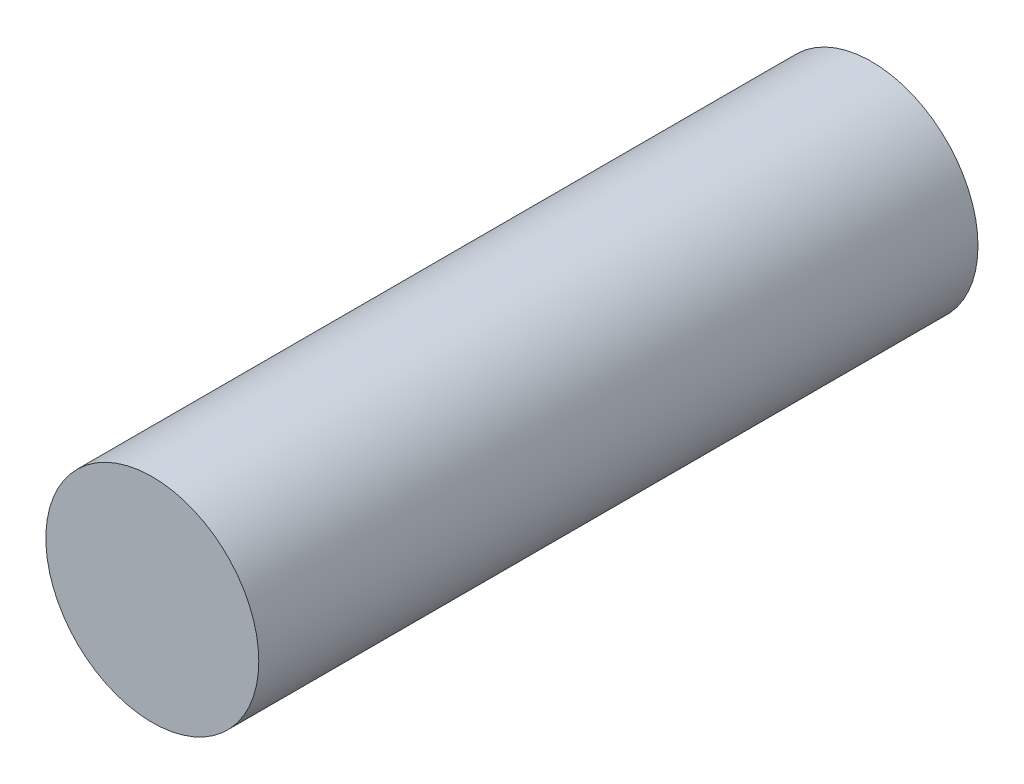
SolidWorks part; units mm, degrees
ref_plane "Front Plane" through (0, 0, 0) normal (0, 0, 1) x (1, 0, 0)
ref_plane "Top Plane" through (0, 0, 0) normal (0, 1, 0) x (1, 0, 0)
ref_plane "Right Plane" through (0, 0, 0) normal (1, 0, 0) x (0, 0, -1)
sketch "Sketch1" plane through (0, 0, 0) normal (0, 0, 1) x (1, 0, 0)
  circle A0 centre (0, 0) radius 4.7752
  dimension "D1" = 9.5504
extrude "Boss-Extrude1" add sketch "Sketch1" along normal blind 32.258
